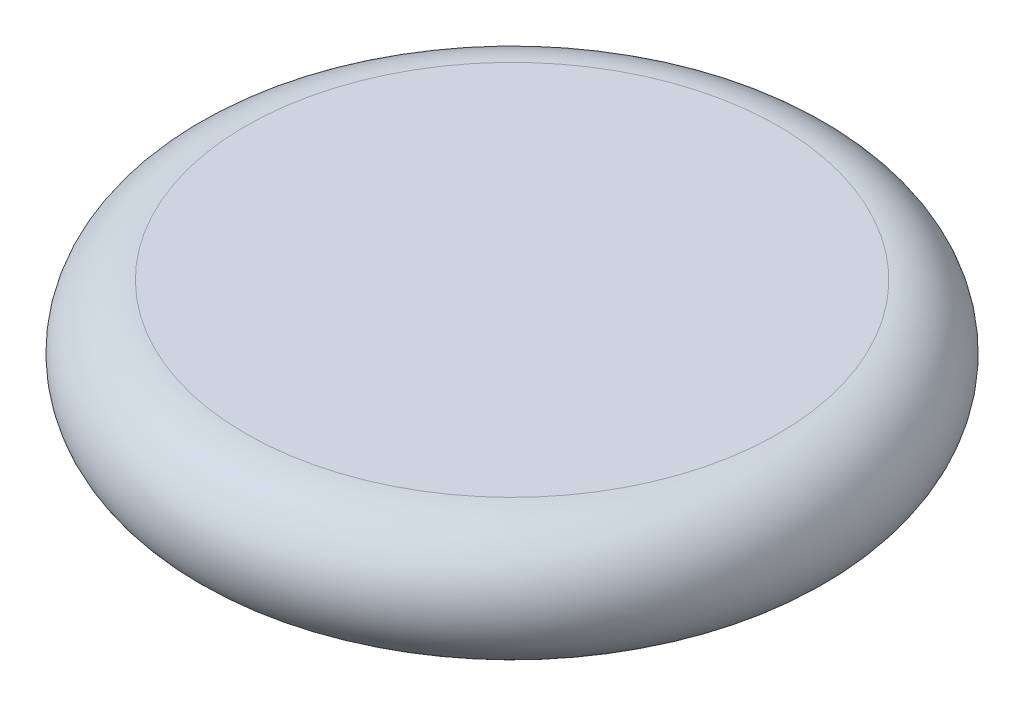
SolidWorks part; units mm, degrees
ref_plane "Front Plane" through (0, 0, 0) normal (0, 0, 1) x (1, 0, 0)
ref_plane "Top Plane" through (0, 0, 0) normal (0, 1, 0) x (1, 0, 0)
ref_plane "Right Plane" through (0, 0, 0) normal (1, 0, 0) x (0, 0, -1)
sketch "Sketch2" plane through (0, 0, 0) normal (0, 0, 1) x (1, 0, 0)
  line L1 (0, 0) -> (40, 0)
  line L2 (0, 0) -> (0, -19)
  line L3 (0, -19) -> (40, -19)
  arc A0 (40, 0) -> (40, -19) centre (40, -9.5) cw
  dimension "D1" = 19
  dimension "D2" = 40
revolve "Revolve1" add sketch "Sketch2" angle 360 about L2
